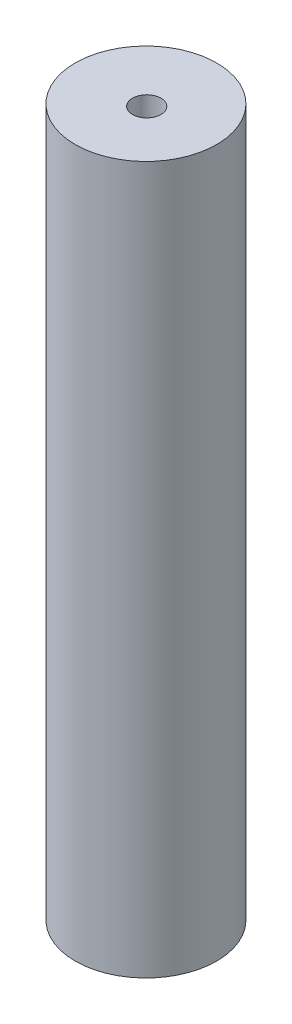
SolidWorks part; units mm, degrees
ref_plane "Front Plane" through (0, 0, 0) normal (0, 0, 1) x (1, 0, 0)
ref_plane "Top Plane" through (0, 0, 0) normal (0, 1, 0) x (1, 0, 0)
ref_plane "Right Plane" through (0, 0, 0) normal (1, 0, 0) x (0, 0, -1)
sketch "Sketch2" plane through (0, 0, 0) normal (0, 1, 0) x (1, 0, 0)
  circle A0 centre (0, 0) radius 12.7
extrude "Boss-Extrude1" add sketch "Sketch2" along normal blind 127
hole_wizard "1/4-20 Tapped Hole1" positions "Sketch5" profile "Sketch4" tap size "1/4-20" standard "Ansi Inch"
sketch "Sketch5" plane through (0, 127, 0) normal (0, 1, 0) x (-1, 0, 0)
  point P0 (-0.4739, 0.3329)
sketch "Sketch4" plane through (0.4739, 127, 0.3329) normal (1, 0, 0) x (0, 0, 1)
  line L0 (0, 0) -> (0, 33.2838)
  line L1 (0, 33.2838) -> (2.5527, 31.75)
  line L2 (2.5527, 31.75) -> (2.5527, 0)
  line L5 (2.5527, 0) -> (0, 0)
  line L10 (0, 33.2838) -> (-2.5527, 31.75) construction
  line L11 (0, -6.35) -> (0, 107.95) construction
  dimension "Tap Drill Dia." = 5.1054
  dimension "Tap Drill Depth" = 31.75
  dimension "Drill Angle" = 118
cosmetic thread "Hole Thread1" parameters "D1"=25.4, "D2"=6.35
ref_plane "Plane1" through (0, 63.5, 0) normal (0, 1, 0) x (-1, 0, 0)
mirror "Mirror1" about plane through (0, 63.5, 0) normal (0, 1, 0) of "1/4-20 Tapped Hole1"
